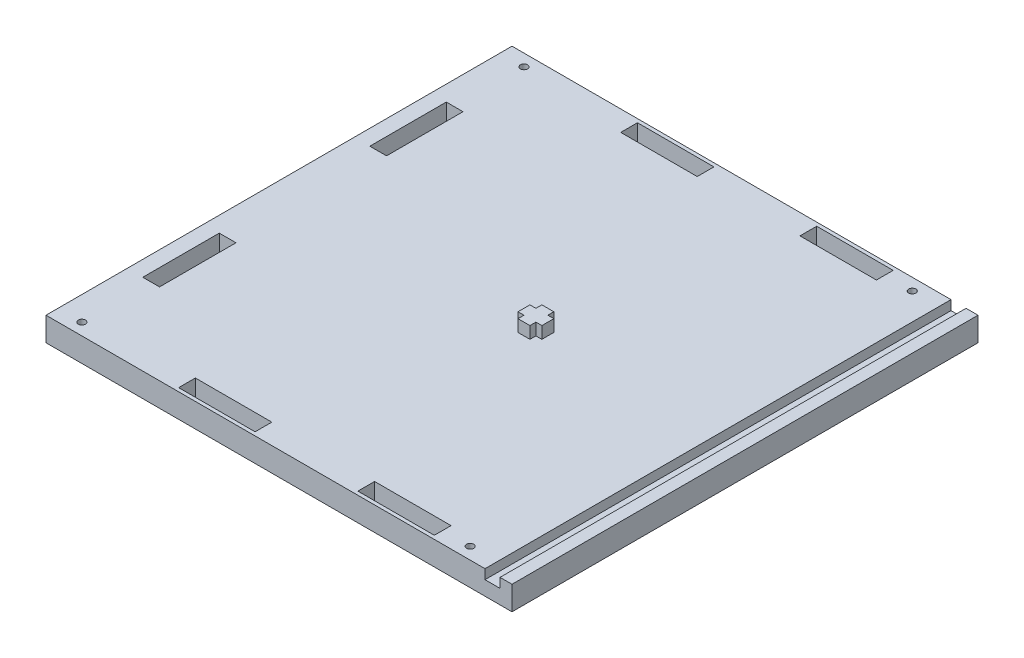
SolidWorks part; units mm, degrees
material "ABS"
ref_plane "Plano frontal" through (0, 0, 0) normal (0, 0, 1) x (1, 0, 0)
ref_plane "Plano superior" through (0, 0, 0) normal (0, 1, 0) x (1, 0, 0)
ref_plane "Plano direito" through (0, 0, 0) normal (1, 0, 0) x (0, 0, -1)
sketch "Esboço1" plane through (0, 0, 0) normal (0, 1, 0) x (1, 0, 0)
  line L1 (97.5, -97.5) -> (-97.5, -97.5)
  line L2 (97.5, -97.5) -> (97.5, 97.5)
  line L3 (97.5, 97.5) -> (-97.5, 97.5)
  line L4 (-97.5, -97.5) -> (-97.5, 97.5)
  line L5 (97.5, -97.5) -> (-97.5, 97.5) construction
  line L6 (97.5, 97.5) -> (-97.5, -97.5) construction
  point P0 (0, 0)
  dimension "D1" = 195
  dimension "D2" = 195
extrude "Ressalto-extrusão1" add sketch "Esboço1" along normal blind 10
sketch "Esboço2" plane through (0, 10, 0) normal (0, 1, 0) x (1, 0, 0)
  line L0 (-121.0573, 0) -> (118.2209, 0) construction
  line L1 (0, 101.1398) -> (0, -101.6578) construction
  line L2 (97.5, 97.5) -> (-97.5, 97.5) construction
  line L3 (-91, 63.5) -> (-84, 63.5)
  line L4 (-91, 63.5) -> (-91, 31.5)
  line L5 (-91, 31.5) -> (-84, 31.5)
  line L6 (-84, 63.5) -> (-84, 31.5)
  line L7 (-91, 63.5) -> (-84, 31.5) construction
  line L8 (-91, 31.5) -> (-84, 63.5) construction
  line L9 (-97.5, 97.5) -> (-97.5, -97.5) construction
  line L10 (-91, -31.5) -> (-84, -63.5) construction
  line L11 (-91, -63.5) -> (-84, -31.5) construction
  line L12 (-84, -63.5) -> (-84, -31.5)
  line L13 (-91, -31.5) -> (-84, -31.5)
  line L14 (-91, -63.5) -> (-91, -31.5)
  line L15 (-91, -63.5) -> (-84, -63.5)
  line L16 (-97.5, -97.5) -> (97.5, -97.5) construction
  line L17 (-43.5, -96) -> (-11.5, -96)
  line L18 (-43.5, -96) -> (-43.5, -89)
  line L19 (-43.5, -89) -> (-11.5, -89)
  line L20 (-11.5, -96) -> (-11.5, -89)
  line L21 (-43.5, -96) -> (-11.5, -89) construction
  line L22 (-43.5, -89) -> (-11.5, -96) construction
  line L23 (97.5, -97.5) -> (97.5, 97.5) construction
  line L24 (63.5, -96) -> (31.5, -96)
  line L29 (63.5, 89) -> (31.5, 96) construction
  line L30 (63.5, 96) -> (31.5, 89) construction
  line L35 (-43.5, 89) -> (-11.5, 96) construction
  line L36 (-43.5, 96) -> (-11.5, 89) construction
  line L41 (63.5, -96) -> (63.5, -89)
  line L42 (63.5, -89) -> (31.5, -89)
  line L43 (31.5, -96) -> (31.5, -89)
  line L44 (63.5, -96) -> (31.5, -89) construction
  line L45 (63.5, -89) -> (31.5, -96) construction
  line L46 (31.5, 96) -> (31.5, 89)
  line L47 (63.5, 89) -> (31.5, 89)
  line L48 (63.5, 96) -> (63.5, 89)
  line L49 (63.5, 96) -> (31.5, 96)
  line L50 (-11.5, 96) -> (-11.5, 89)
  line L51 (-43.5, 89) -> (-11.5, 89)
  line L52 (-43.5, 96) -> (-43.5, 89)
  line L53 (-43.5, 96) -> (-11.5, 96)
  point P4 (-87.5, 47.5)
  point P18 (-87.5, -47.5)
  point P19 (-27.5, -92.5)
  point P26 (47.5, -92.5)
  point P39 (47.5, 92.5)
  point P40 (-27.5, 92.5)
  dimension "D1" = 7
  dimension "D2" = 32
  dimension "D3" = 50
  dimension "D4" = 6.5
  dimension "D5" = 70
  dimension "D6" = 1.5
  dimension "D7" = 1.5
  dimension "D8" = 50
extrude "Corte-extrusão1" cut sketch "Esboço2" against normal through all
sketch "Esboço3" plane through (0, 10, 0) normal (0, 1, 0) x (1, 0, 0)
  line L0 (-115.6253, 0) -> (116.1427, 0) construction
  line L1 (92.5, -97.5) -> (86.2, -97.5)
  line L2 (92.5, -97.5) -> (92.5, 97.5)
  line L3 (92.5, 97.5) -> (86.2, 97.5)
  line L4 (86.2, -97.5) -> (86.2, 97.5)
  line L5 (92.5, -97.5) -> (86.2, 97.5) construction
  line L6 (92.5, 97.5) -> (86.2, -97.5) construction
  line L7 (97.5, 97.5) -> (-97.5, 97.5) construction
  line L8 (97.5, -97.5) -> (97.5, 97.5) construction
  point P0 (89.35, 0)
  dimension "D1" = 5
  dimension "D2" = 6.3
extrude "Corte-extrusão2" cut sketch "Esboço3" against normal blind 4
sketch "Esboço4" plane through (0, 0, 0) normal (0, -1, 0) x (1, 0, 0)
  line L0 (-97.5, 97.5) -> (97.5, 97.5) construction
  line L1 (-97.5, -97.5) -> (-97.5, 97.5) construction
  line L2 (-114.0099, 0) -> (126.5738, 0) construction
  circle A0 centre (-87.5, 92.5) radius 1.5
  circle A1 centre (-87.5, -92.5) radius 1.5
  dimension "D1" = 3
  dimension "D2" = 5
  dimension "D3" = 10
extrude "Corte-extrusão3" cut sketch "Esboço4" against normal through all
sketch "Esboço5" plane through (0, 0, 0) normal (0, -1, 0) x (1, 0, 0)
  line L0 (75, 116.8309) -> (75, -117.7427) construction
  line L1 (-97.5, 97.5) -> (97.5, 97.5) construction
  line L2 (-113.9686, 0) -> (124.33, 0) construction
  line L3 (-87.5, 107.3478) -> (-87.5, -108.1252) construction
  line L4 (-97.5, -97.5) -> (-97.5, 97.5) construction
  line L6 (97.5, 97.5) -> (97.5, -97.5) construction
  circle A0 centre (75, 92.5) radius 1.5
  circle A1 centre (75, -92.5) radius 1.5
  dimension "D1" = 3
  dimension "D2" = 5
  dimension "D3" = 10
  dimension "D4" = 22.5
extrude "Corte-extrusão4" cut sketch "Esboço5" against normal through all
sketch "Esboço6" plane through (0, 10, 0) normal (0, 1, 0) x (1, 0, 0)
  line L0 (-77.5, 103.9851) -> (-77.5, -106.0674) construction
  line L1 (-97.5, 97.5) -> (-97.5, -97.5) construction
  line L2 (10, 102.4331) -> (10, -105.0921) construction
  line L3 (97.5, -97.5) -> (97.5, 97.5) construction
  line L4 (-113.8146, 0) -> (113.8323, 0) construction
  line L6 (15, -2.5) -> (5, -2.5)
  line L7 (15, -2.5) -> (15, 2.5)
  line L8 (15, 2.5) -> (5, 2.5)
  line L9 (5, -2.5) -> (5, 2.5)
  line L10 (15, -2.5) -> (5, 2.5) construction
  line L11 (15, 2.5) -> (5, -2.5) construction
  line L12 (12.5, -5) -> (7.5, -5)
  line L13 (12.5, -5) -> (12.5, 5)
  line L14 (12.5, 5) -> (7.5, 5)
  line L15 (7.5, -5) -> (7.5, 5)
  line L16 (12.5, -5) -> (7.5, 5) construction
  line L17 (12.5, 5) -> (7.5, -5) construction
  point P10 (10, 0)
  point P19 (10, 0)
  dimension "D1" = 20
  dimension "D2" = 87.5
  dimension "D3" = 10
  dimension "D4" = 5
  dimension "D5" = 10
  dimension "D6" = 5
extrude "Ressalto-extrusão2" add sketch "Esboço6" along normal blind 5 contours L15 L12 L13 L6 | L15 L6 L13 L8 | L13 L6 L7 L8 | L6 L15 L8 L9 | L15 L8 L13 L14
